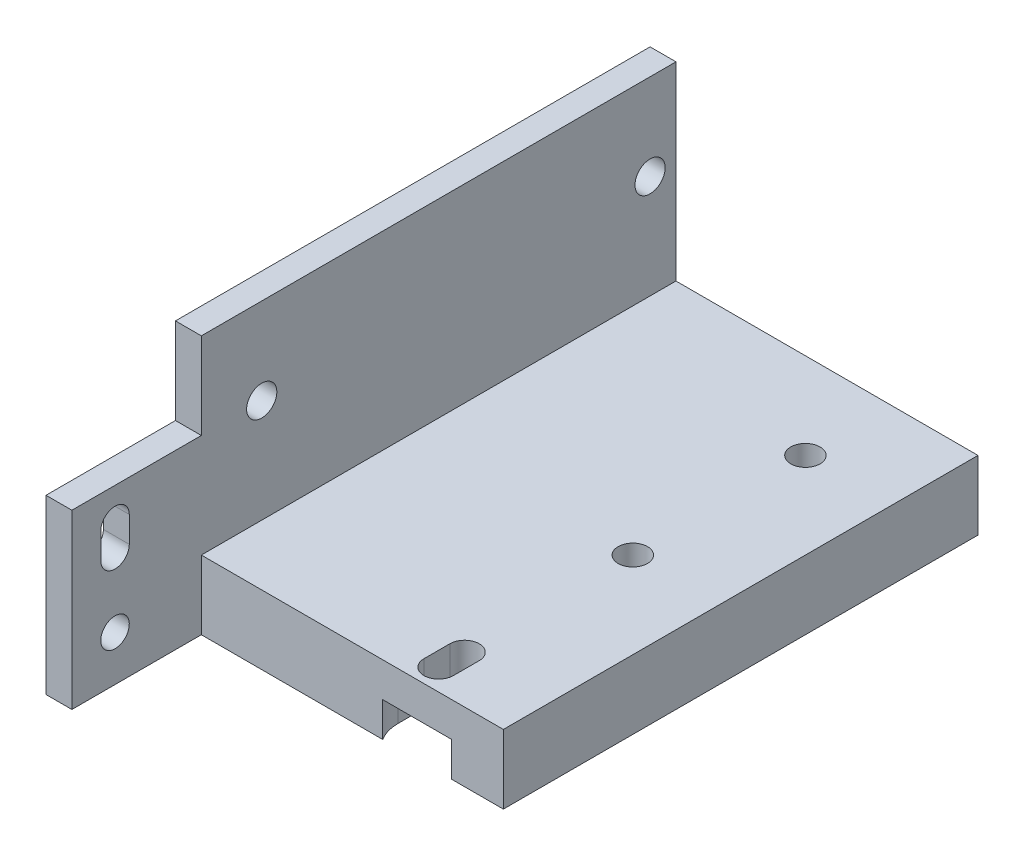
SolidWorks part; units mm, degrees
ref_plane "Plano frontal" through (0, 0, 0) normal (0, 0, 1) x (1, 0, 0)
ref_plane "Plano superior" through (0, 0, 0) normal (0, 1, 0) x (1, 0, 0)
ref_plane "Plano direito" through (0, 0, 0) normal (1, 0, 0) x (0, 0, -1)
sketch "Esboço1" plane through (0, 0, 0) normal (0, 0, 1) x (1, 0, 0)
  line L0 (0, 0) -> (38, 0)
  line L1 (38, 0) -> (38, 8)
  line L2 (38, 8) -> (3, 8)
  line L3 (3, 8) -> (3, 30)
  line L4 (3, 30) -> (0, 30)
  line L5 (0, 30) -> (0, 0)
  dimension "D1" = 8
  dimension "D2" = 3
  dimension "D3" = 35
  dimension "D4" = 30
extrude "Ressalto-extrusão1" add sketch "Esboço1" along normal blind 55
sketch "Esboço2" plane through (0, 0, 0) normal (0, -1, 0) x (1, 0, 0)
  line L0 (0, 0) -> (38, 0) construction
  line L1 (20.4, 42.6) -> (35.6, 42.6)
  line L2 (20.4, 42.6) -> (20.4, 17.4)
  line L3 (20.4, 17.4) -> (35.6, 17.4)
  line L4 (35.6, 42.6) -> (35.6, 17.4)
  line L5 (20.4, 42.6) -> (35.6, 17.4) construction
  line L6 (20.4, 17.4) -> (35.6, 42.6) construction
  line L7 (38, 55) -> (38, 0) construction
  point P0 (28, 30)
  dimension "D1" = 25.2
  dimension "D2" = 15.2
  dimension "D3" = 10
  dimension "D4" = 30
extrude "Corte-extrusão1" cut sketch "Esboço2" against normal blind 3
sketch "Esboço4" plane through (0, 0, 0) normal (0, -1, 0) x (1, 0, 0)
  line L0 (35.6, 42.6) -> (20.4, 42.6) construction
  line L1 (20.4, 42.6) -> (20.4, 17.4) construction
  line L2 (28, 51) -> (28, 10) construction
  line L3 (28, 52.5) -> (28, 49.5) construction
  line L4 (29.7, 52.5) -> (29.7, 49.5)
  line L5 (26.3, 52.5) -> (26.3, 49.5)
  circle A0 centre (28, 30) radius 1.7
  arc A1 (29.7, 52.5) -> (26.3, 52.5) centre (28, 52.5) ccw
  circle A2 centre (28, 10) radius 1.7
  arc A3 (26.3, 49.5) -> (29.7, 49.5) centre (28, 49.5) ccw
  point P5 (28, 42.6)
  point P9 (20.4, 30)
  point P14 (28, 51)
  dimension "D1" = 3.4
  dimension "D2" = 41
  dimension "D3" = 3
  dimension "D4" = 20
extrude "Corte-extrusão2" cut sketch "Esboço4" against normal through all
sketch "Esboço5" plane through (0, 0, 0) normal (0, -1, 0) x (1, 0, 0)
  line L6 (32.7, 49.5) -> (32.7, 52.5)
  line L7 (23.3, 52.5) -> (23.3, 49.5)
  line L8 (32.7, 49.5) -> (32.7, 52.5)
  line L9 (23.3, 52.5) -> (23.3, 49.5)
  arc A6 (23.3, 49.5) -> (32.7, 49.5) centre (28, 49.5) ccw
  arc A7 (32.7, 52.5) -> (23.3, 52.5) centre (28, 52.5) ccw
  arc A8 (23.3, 49.5) -> (32.7, 49.5) centre (28, 49.5) ccw
  arc A9 (32.7, 52.5) -> (23.3, 52.5) centre (28, 52.5) ccw
  circle A10 centre (28, 10) radius 4.7
  circle A11 centre (28, 10) radius 4.7
  point P1 (18.3, 52.8972)
  point P10 (0, 0)
  dimension "D1" = 3
  dimension "D2" = 3
extrude "Corte-extrusão3" cut sketch "Esboço5" against normal blind 4
sketch "Esboço6" plane through (0, 0, 0) normal (-1, 0, 0) x (0, 0, 1)
  line L0 (55, 0) -> (0, 0) construction
  line L1 (48, 20) -> (3, 20) construction
  line L3 (0, 30) -> (0, 0) construction
  circle A0 centre (48, 20) radius 1.75
  circle A1 centre (3, 20) radius 1.75
  dimension "D3" = 3.5
  dimension "D1" = 20
  dimension "D2" = 45
  dimension "D4" = 3
extrude "Corte-extrusão4" cut sketch "Esboço6" against normal blind 4
sketch "Esboço7" plane through (0, 0, 0) normal (-1, 0, 0) x (0, 0, 1)
  line L0 (55, 0) -> (70, 0)
  line L1 (70, 0) -> (70, 20)
  line L2 (70, 20) -> (55, 20)
  line L3 (55, 30) -> (55, 0) construction
  line L4 (55, 20) -> (55, 0)
  line L5 (65, 13.25) -> (65, 16.25) construction
  line L6 (63.35, 13.25) -> (63.35, 16.25)
  line L7 (66.65, 13.25) -> (66.65, 16.25)
  line L8 (65, 14.75) -> (65, 5.25) construction
  circle A0 centre (65, 5.25) radius 1.65
  arc A1 (63.35, 13.25) -> (66.65, 13.25) centre (65, 13.25) ccw
  arc A2 (66.65, 16.25) -> (63.35, 16.25) centre (65, 16.25) ccw
  point P12 (65, 14.75)
  point P18 (65, 10)
  point P19 (70, 10)
  dimension "D5" = 3.3
  dimension "D1" = 15
  dimension "D2" = 20
  dimension "D3" = 9.5
  dimension "D4" = 3
  dimension "D6" = 5
extrude "Ressalto-extrusão2" add sketch "Esboço7" against normal up to surface (3 mm away) up to face at (3, 20, 4.75)
